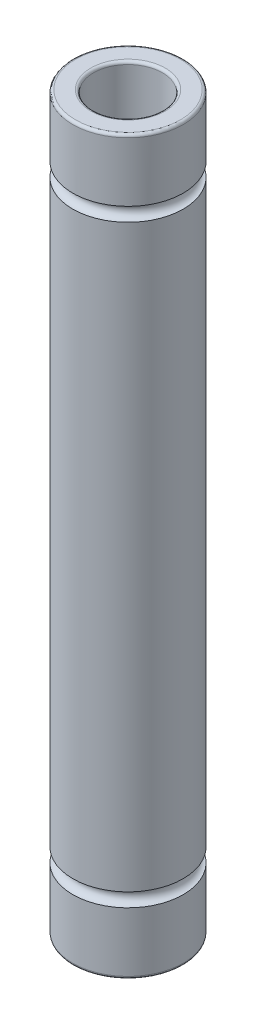
SolidWorks part; units mm, degrees
ref_plane "Front Plane" through (0, 0, 0) normal (0, 0, 1) x (1, 0, 0)
ref_plane "Top Plane" through (0, 0, 0) normal (0, 1, 0) x (1, 0, 0)
ref_plane "Right Plane" through (0, 0, 0) normal (1, 0, 0) x (0, 0, -1)
sketch "Sketch1" plane through (0, 0, 0) normal (0, 1, 0) x (1, 0, 0)
  circle A0 centre (0, 0) radius 2.5
  circle A1 centre (0, 0) radius 4
  dimension "D1" = 5
  dimension "D2" = 8
extrude "Boss-Extrude1" add sketch "Sketch1" along normal mid plane 53
sketch "Sketch2" plane through (0, 0, 0) normal (0, 0, 1) x (1, 0, 0)
  line L0 (4, -26.5) -> (4, 26.5) construction
  line L2 (0, 35.3745) -> (0, -37.5822) construction
  line L3 (0, -4.4) -> (0, 4.4) construction
  circle A0 centre (4, -21.5) radius 0.5
  dimension "D2" = 1
  dimension "D1" = 5
revolve "Cut-Revolve1" cut sketch "Sketch2" angle 360 about L2
sketch "Sketch3" plane through (0, 0, 0) normal (0, 0, 1) x (1, 0, 0)
  line L0 (-12.5354, 0) -> (20.7066, 0) construction
  line L1 (4.4, 0) -> (-4.4, 0) construction
  line L3 (4, 26.5) -> (-4, 26.5) construction
  line L4 (-4, -26.5) -> (4, -26.5) construction
mirror "Mirror1" about plane through (0, 0, 0) normal (0, 1, 0) of "Cut-Revolve1"
fillet "Fillet1" radius 0.2 4 edges at (0, 26.5, 4) (0, 26.5, 2.5) (0, -26.5, 2.5) (0, -26.5, 4)
